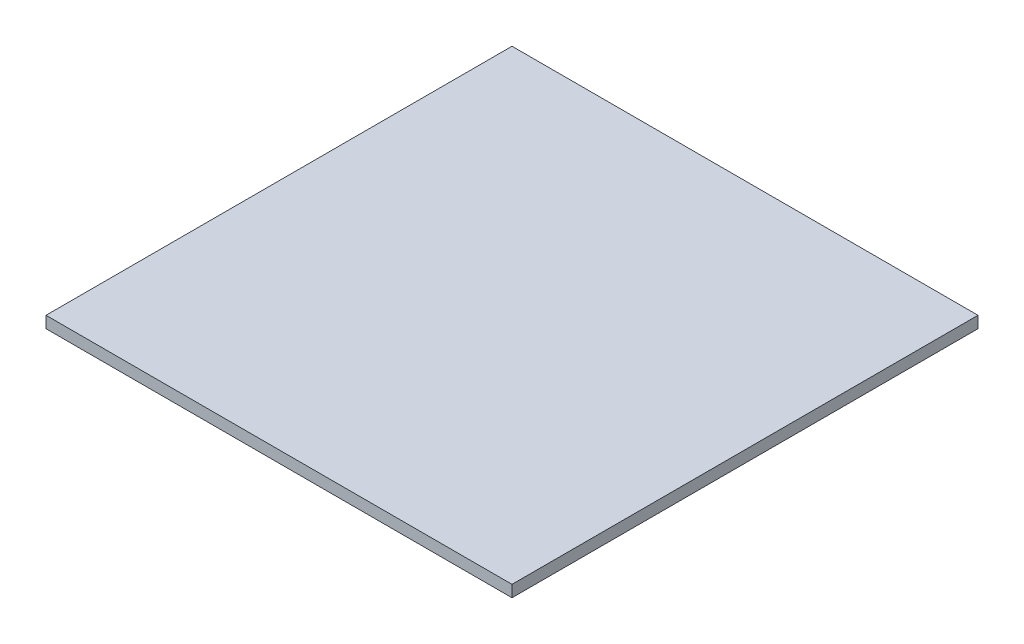
SolidWorks part; units mm, degrees
material "Glass"
ref_plane "Front Plane" through (0, 0, 0) normal (0, 0, 1) x (1, 0, 0)
ref_plane "Top Plane" through (0, 0, 0) normal (0, 1, 0) x (1, 0, 0)
ref_plane "Right Plane" through (0, 0, 0) normal (1, 0, 0) x (0, 0, -1)
sketch "Sketch1" plane through (0, 0, 0) normal (0, 1, 0) x (1, 0, 0)
  line L0 (0, 200) -> (0, -200) construction
  line L1 (-200, 200) -> (200, 200)
  line L2 (-200, 200) -> (-200, -200)
  line L3 (-200, -200) -> (200, -200)
  line L4 (200, 200) -> (200, -200)
  line L5 (-200, 0) -> (200, 0) construction
  dimension "D1" = 400
  dimension "D2" = 400
  dimension "D3" = 0
  dimension "D4" = 0
extrude "Boss-Extrude1" add sketch "Sketch1" along normal blind 10
